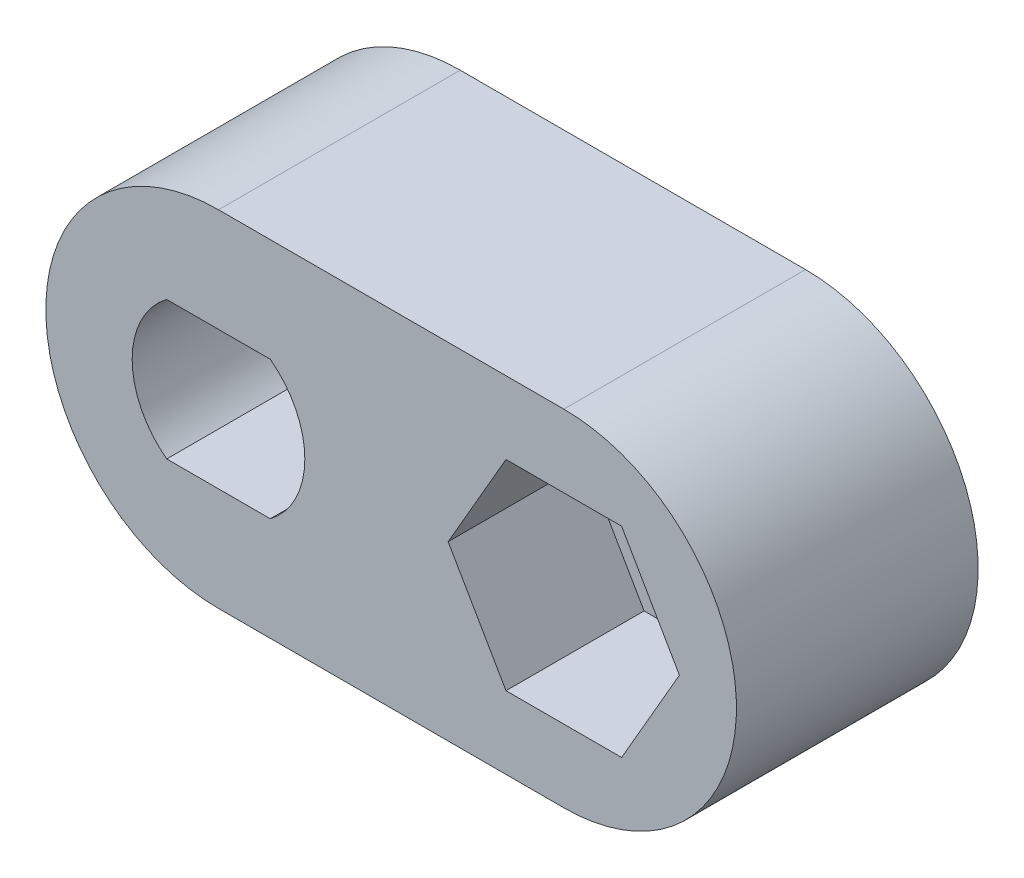
SolidWorks part; units mm, degrees
ref_plane "前视基准面" through (0, 0, 0) normal (0, 0, 1) x (1, 0, 0)
ref_plane "上视基准面" through (0, 0, 0) normal (0, 1, 0) x (1, 0, 0)
ref_plane "右视基准面" through (0, 0, 0) normal (1, 0, 0) x (0, 0, -1)
sketch "草图1" plane through (0, 0, 0) normal (0, 0, 1) x (1, 0, 0)
  line L0 (0, 0) -> (10, 0) construction
  line L1 (0, 5) -> (10, 5)
  line L2 (0, -5) -> (10, -5)
  arc A0 (0, 5) -> (0, -5) centre (0, 0) ccw
  arc A1 (10, -5) -> (10, 5) centre (10, 0) ccw
  point P3 (5, 0)
  dimension "D2" = 5
  dimension "D1" = 10
extrude "凸台-拉伸1" add sketch "草图1" along normal blind 7
sketch "草图2" plane through (0, 0, 7) normal (0, 0, 1) x (1, 0, 0)
  line L0 (0, 0) -> (3.4403, 0) construction
  line L1 (-1.5, 2) -> (1.5, 2)
  line L2 (-1.5, -2) -> (1.5, -2)
  circle A0 centre (0, 0) radius 2.5
  dimension "D1" = 5
  dimension "D2" = 2
extrude "切除-拉伸1" cut sketch "草图2" against normal blind 4
hole_wizard "M3 六角凹锥坑螺钉的锥形沉头孔1" positions "草图3" profile "草图4" countersink size "M3" standard "ISO"
sketch "草图3" plane through (0, 0, 0) normal (0, 0, -1) x (-1, 0, 0)
  point P0 (0, 0)
sketch "草图4" plane through (0, 0, 0) normal (1, 0, 0) x (0, 1, 0)
  line L0 (0, 0) -> (0, 8.5215)
  line L1 (0, 8.5215) -> (1.7, 7.5)
  line L2 (1.7, 7.5) -> (1.7, 1.66)
  line L3 (1.7, 1.66) -> (3.36, 0)
  line L5 (3.36, 0) -> (0, 0)
  line L6 (-1.7, 1.66) -> (-3.36, 0) construction
  line L10 (0, 8.5215) -> (-1.7, 7.5) construction
  line L11 (0, -6.35) -> (0, 107.95) construction
  dimension "孔直径" = 3.4
  dimension "孔深度" = 7.5
  dimension "近端锥形沉头孔直径" = 6.72
  dimension "近端锥形沉头孔角度" = 90
  dimension "导头角度" = 118
hole_wizard "孔1" positions "草图5" profile "草图6" legacy end condition through all
sketch "草图5" plane through (0, 0, 0) normal (0, 0, -1) x (-1, 0, 0)
  point P0 (-10, 0)
sketch "草图6" plane through (10, 0, 0) normal (1, 0, 0) x (0, 1, 0)
  line L0 (0, 0) -> (0, 7)
  line L1 (0, 7) -> (2.075, 7)
  line L2 (2.075, 7) -> (2.075, 0)
  line L3 (2.075, 0) -> (0, 0)
  line L4 (0, 110) -> (0, -10) construction
  dimension "直径" = 4.15
  dimension "深度" = 7
sketch "草图7" plane through (0, 0, 7) normal (0, 0, 1) x (1, 0, 0)
  line L1 (8.3257, -2.9) -> (11.6743, -2.9)
  line L2 (11.6743, -2.9) -> (13.3486, 0)
  line L3 (13.3486, 0) -> (11.6743, 2.9)
  line L4 (11.6743, 2.9) -> (8.3257, 2.9)
  line L5 (8.3257, 2.9) -> (6.6514, 0)
  line L6 (6.6514, 0) -> (8.3257, -2.9)
  circle A0 centre (10, 0) radius 2.9 construction
  dimension "D1" = 5.8
extrude "切除-拉伸2" cut sketch "草图7" against normal blind 4
